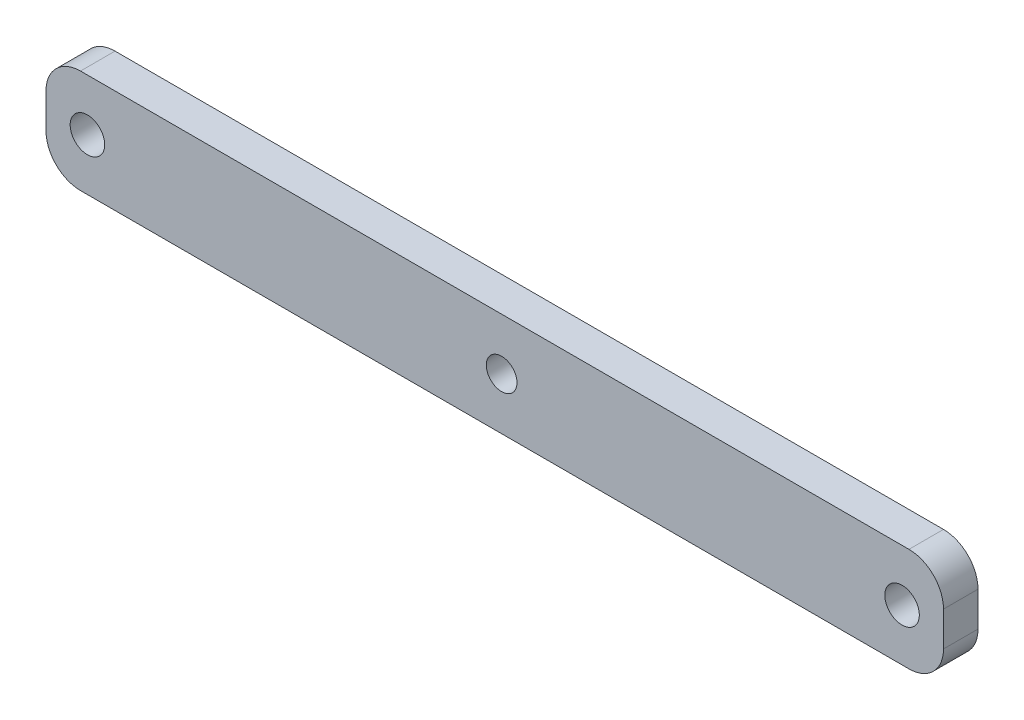
SolidWorks part; units mm, degrees
ref_plane "Спереди" through (0, 0, 0) normal (0, 0, 1) x (1, 0, 0)
ref_plane "Сверху" through (0, 0, 0) normal (0, 1, 0) x (1, 0, 0)
ref_plane "Справа" through (0, 0, 0) normal (1, 0, 0) x (0, 0, -1)
other "Configuration Table"
sketch "Sketch20" plane through (0, 0, 0) normal (0, 0, 1) x (1, 0, 0)
  line L0 (-21.9862, -1.9998) -> (98.0138, -1.9998)
  line L1 (103.0138, -6.9998) -> (103.0138, -11.9998)
  line L2 (98.0138, -16.9998) -> (-21.9862, -16.9998)
  line L3 (-26.9862, -11.9998) -> (-26.9862, -6.9998)
  line L4 (38.0138, 14.1911) -> (38.0138, -20.3289) construction
  arc A0 (98.0138, -1.9998) -> (103.0138, -6.9998) centre (98.0138, -6.9998) cw
  arc A1 (103.0138, -11.9998) -> (98.0138, -16.9998) centre (98.0138, -11.9998) cw
  arc A2 (-21.9862, -16.9998) -> (-26.9862, -11.9998) centre (-21.9862, -11.9998) cw
  arc A3 (-26.9862, -6.9998) -> (-21.9862, -1.9998) centre (-21.9862, -6.9998) cw
  circle A4 centre (-20.9862, -9.4998) radius 2.5
  circle A5 centre (97.0138, -9.4998) radius 2.5
  circle A6 centre (39.0138, -9.4998) radius 2.2234
  point P14 (-26.9862, -9.4998)
  point P21 (0, 0)
  point P22 (-0.9862, -9.4998)
  point P23 (0, 0)
  point P24 (38.0138, -1.9998)
  dimension "D5" = 5
  dimension "D1" = 60
  dimension "D3" = 120
  dimension "D4" = 6
  dimension "D6" = 15
extrude "Boss-Extrude3" add sketch "Sketch20" along normal blind 5
